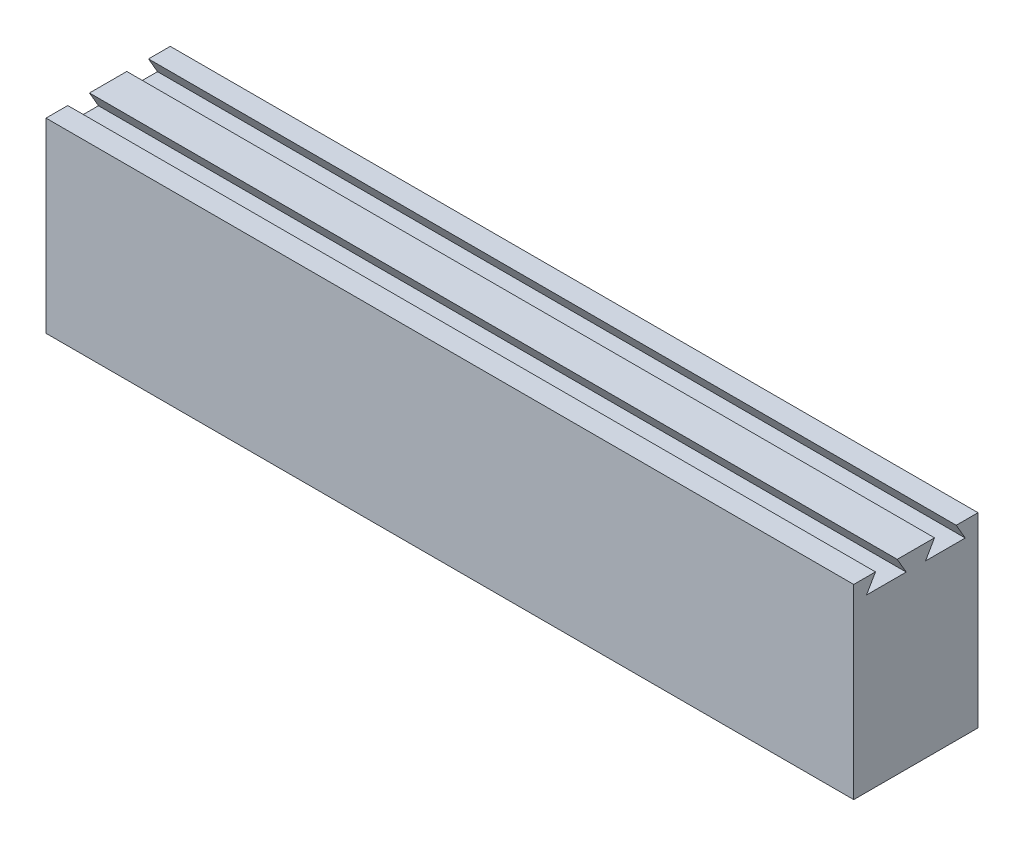
SolidWorks part; units mm, degrees
ref_plane "Front Plane" through (0, 0, 0) normal (0, 0, 1) x (1, 0, 0)
ref_plane "Top Plane" through (0, 0, 0) normal (0, 1, 0) x (1, 0, 0)
ref_plane "Right Plane" through (0, 0, 0) normal (1, 0, 0) x (0, 0, -1)
sketch "Sketch1" plane through (0, 0, 0) normal (1, 0, 0) x (0, 0, -1)
  line L0 (3, 15) -> (1.555, 12.4972)
  line L1 (-10, -15) -> (10, -15)
  line L2 (-10, -15) -> (-10, 15)
  line L3 (-10, 15) -> (10, 15)
  line L4 (10, -15) -> (10, 15)
  line L5 (-10, -15) -> (10, 15) construction
  line L6 (-10, 15) -> (10, -15) construction
  line L7 (1.555, 12.4972) -> (7.945, 12.4972)
  line L8 (7.945, 12.4972) -> (6.5, 15)
  line L9 (6.5, 15) -> (3, 15)
  line L10 (0, 6.1509) -> (0, 23.8491)
  line L11 (-7.945, 12.4972) -> (-6.5, 15)
  line L12 (-1.555, 12.4972) -> (-7.945, 12.4972)
  line L13 (-3, 15) -> (-1.555, 12.4972)
  line L14 (-6.5, 15) -> (-3, 15)
  point P0 (0, 0)
  point P13 (0, 15)
  dimension "D1" = 20
  dimension "D2" = 30
  dimension "D3" = 3.5
  dimension "D4" = 3.5
  dimension "D5" = 60
  dimension "D6" = 60
  dimension "D7" = 6.39
  dimension "D8" = 2.5028
extrude "Boss-Extrude1" add sketch "Sketch1" along normal mid plane 130
